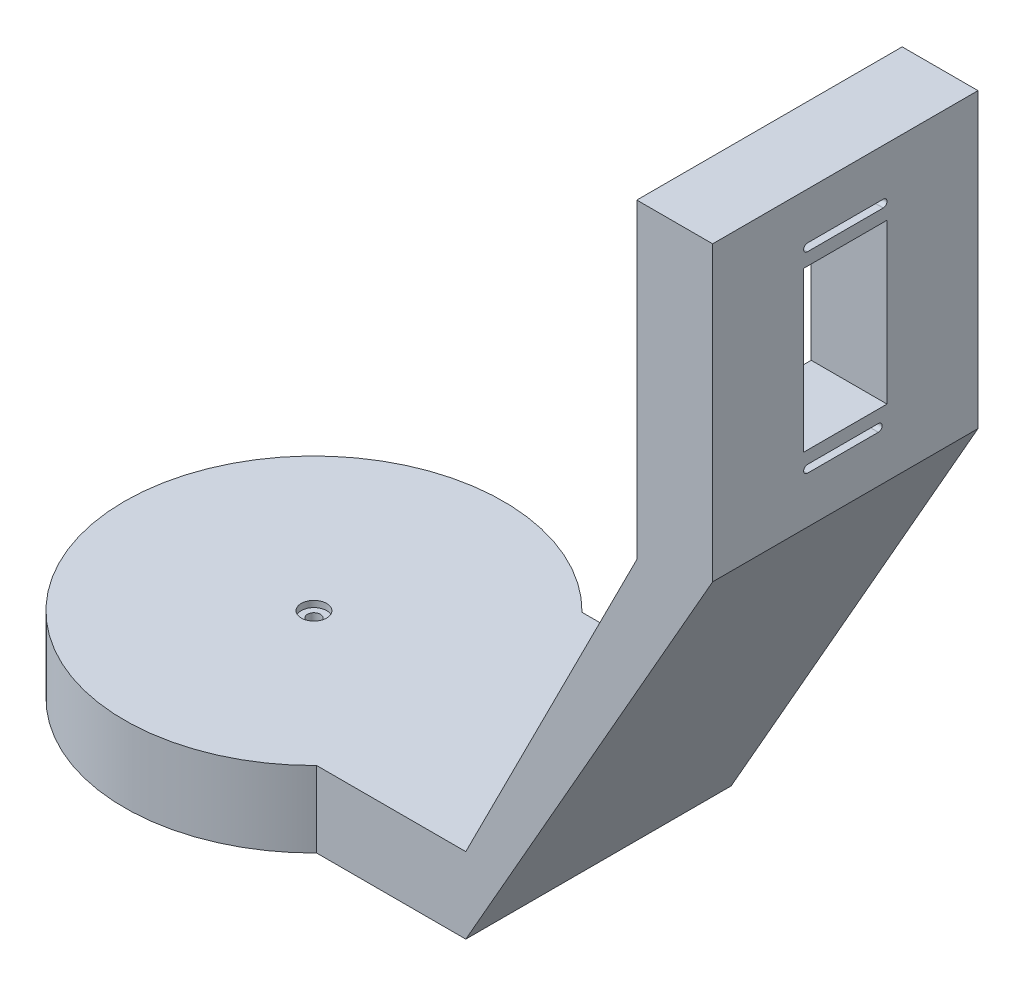
SolidWorks part; units mm, degrees
ref_plane "Front" through (0, 0, 0) normal (0, 0, 1) x (1, 0, 0)
ref_plane "Top" through (0, 0, 0) normal (0, 1, 0) x (1, 0, 0)
ref_plane "Right" through (0, 0, 0) normal (1, 0, 0) x (0, 0, -1)
sketch "草图1" plane through (0, 0, 0) normal (0, 1, 0) x (1, 0, 0)
  line L13 (0.0555, 35) -> (75.0555, 35)
  line L14 (0.0555, 35) -> (0.0555, -35)
  line L15 (0.0555, -35) -> (75.0555, -35)
  line L16 (75.0555, 35) -> (75.0555, -35)
  circle A1 centre (0, 0) radius 50
  dimension "D1" = 100
  dimension "D2" = 35
  dimension "D3" = 35
  dimension "D4" = 75
extrude "凸台-拉伸1" add sketch "草图1" along normal blind 20 contours A1 L15 L16 L13 | L15 A1 L13 L14 | L13 A1 L15 L14
sketch "草图2" plane through (0, 0, 35) normal (0, 0, 1) x (1, 0, 0)
  line L0 (75.0555, 0) -> (140.1741, 114.1921)
  line L1 (140.1741, 114.1921) -> (140.1741, 191.4116)
  line L2 (140.1741, 191.4116) -> (120.1741, 191.4116)
  line L3 (120.1741, 191.4116) -> (120.1741, 109.2863)
  line L5 (120.1741, 109.2863) -> (75.0555, 20)
  line L6 (75.0555, 20) -> (75.0555, 0)
  dimension "D1" = 20
  dimension "D2" = 77.2194
extrude "凸台-拉伸2" add sketch "草图2" against normal blind 70 contours L2 L3 L5 L6 L0 L1
hole_wizard "1/4 六角头螺钉的柱形沉头孔base" positions "草图7" profile "草图8" counterbore size "M3" standard "ANSI Metric" end condition through all
sketch "草图7" plane through (0, 20, 0) normal (0, 1, 0) x (1, 0, 0)
  point P0 (0, 0)
sketch "草图8" plane through (0, 20, 0) normal (1, 0, 0) x (0, 0, 1)
  line L0 (0, 0) -> (0, 20)
  line L1 (0, 20) -> (1.7, 20)
  line L3 (1.7, 20) -> (1.7, 1.65)
  line L4 (1.7, 1.65) -> (3.35, 1.65)
  line L5 (3.35, 1.65) -> (3.35, 0)
  line L7 (3.35, 0) -> (0, 0)
  line L11 (0, -6.35) -> (0, 107.95) construction
  dimension "通孔孔直径" = 3.4
  dimension "通孔孔深度" = 20
  dimension "柱形沉头孔直径" = 6.7
  dimension "柱形沉头孔深度" = 1.65
sketch "草图10" plane through (0, 0, 35) normal (0, 0, 1) x (1, 0, 0)
sketch "草图11" plane through (140.1741, 0, 0) normal (1, 0, 0) x (0, 0, -1)
  line L1 (-11, 173.8016) -> (11, 173.8016)
  line L2 (-11, 173.8016) -> (-11, 131.8016)
  line L3 (-11, 131.8016) -> (11, 131.8016)
  line L4 (11, 173.8016) -> (11, 131.8016)
  line L5 (-35, 114.1921) -> (-35, 191.4116) construction
  line L7 (35, 191.4116) -> (-35, 191.4116) construction
  dimension "D1" = 22
  dimension "D2" = 42
  dimension "D3" = 24
  dimension "D4" = 17.61
extrude "切除-拉伸1" cut sketch "草图11" against normal blind 32
sketch "草图14" plane through (140.1741, 0, 0) normal (1, 0, 0) x (0, 0, -1)
  line L0 (-10, 179.1016) -> (10, 179.1016)
  line L1 (-10, 177.1016) -> (10, 177.1016)
  line L2 (11, 173.8016) -> (-11, 173.8016) construction
  line L3 (-35, 114.1921) -> (-35, 191.4116) construction
  line L6 (-10, 128.5016) -> (8.7063, 128.5016)
  line L7 (-10, 126.5016) -> (8.7063, 126.5016)
  line L8 (-11, 131.8016) -> (11, 131.8016) construction
  arc A0 (-10, 179.1016) -> (-10, 177.1016) centre (-10, 178.1016) ccw
  arc A1 (10, 179.1016) -> (10, 177.1016) centre (10, 178.1016) cw
  arc A4 (-10, 128.5016) -> (-10, 126.5016) centre (-10, 127.5016) ccw
  arc A5 (8.7063, 128.5016) -> (8.7063, 126.5016) centre (8.7063, 127.5016) cw
  dimension "D3" = 25
  dimension "D4" = 3.3
  dimension "D1" = 2
  dimension "D2" = 3.3
  dimension "D5" = 25
extrude "切除-拉伸2" cut sketch "草图14" against normal blind 67
sketch "草图19" plane through (0, 0, 0) normal (0, -1, 0) x (1, 0, 0)
  line L0 (-29.939, 2.9835) -> (0, 6)
  line L1 (29.9255, 2.977) -> (0, 6)
  line L2 (29.8896, -3.02) -> (0, -6)
  line L3 (-30.0737, -4.2635) -> (0, -6)
  arc A2 (29.8896, -3.02) -> (29.9255, 2.977) centre (30, -0.022) ccw
  arc A3 (-30.0737, -4.2635) -> (-29.939, 2.9835) centre (-30, -0.6401) cw
  circle A4 centre (0, 0) radius 6
  dimension "D1" = 30
  dimension "D2" = 30
sketch "草图20" plane through (0, 0, 0) normal (0, -1, 0) x (1, 0, 0)
  line L0 (0, 6) -> (-10.4471, 4.9474)
  line L1 (-29.939, 2.9835) -> (0, 6) construction
  line L2 (-10.4471, 4.9474) -> (-10.4471, -5.3968)
  line L3 (-30.0737, -4.2635) -> (0, -6) construction
  line L4 (-10.4471, -5.3968) -> (0, -6)
  line L6 (0, -6) -> (10.4468, -4.9584)
  line L7 (29.8896, -3.02) -> (0, -6) construction
  line L8 (10.4468, -4.9584) -> (10.4468, 4.9447)
  line L9 (29.9255, 2.977) -> (0, 6) construction
  line L10 (10.4468, 4.9447) -> (0, 6)
  point P11 (0, 0)
  point P18 (0, 0)
  point P19 (0, 0)
  point P20 (0, 0)
  point P21 (0, 0)
  point P22 (0, 0)
  point P23 (2.4865, -5.7521)
  dimension "D1" = 10.5
  dimension "D2" = 10.5
extrude "切除-拉伸3" cut sketch "草图19" against normal blind 2 contours L1 L0 A3 L3 L2 A2
extrude "切除-拉伸4" cut sketch "草图20" against normal blind 3.5
